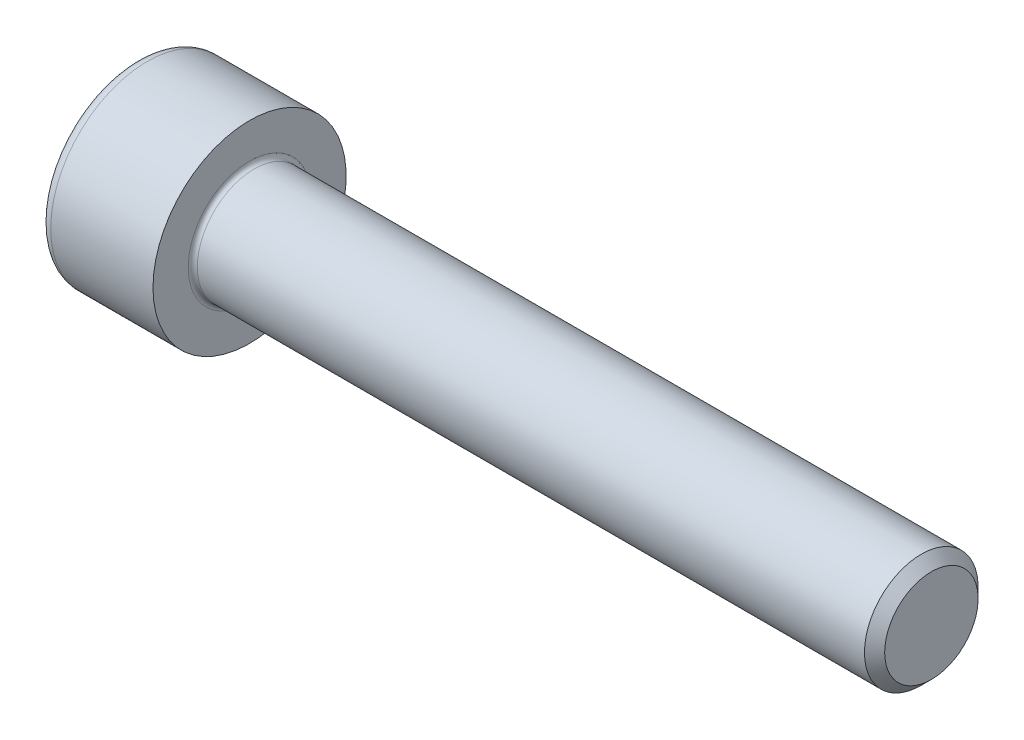
SolidWorks part; units mm, degrees
ref_plane "Plane1" through (0, 0, 0) normal (0, 0, 1) x (1, 0, 0)
ref_plane "Plane2" through (0, 0, 0) normal (0, 1, 0) x (1, 0, 0)
ref_plane "Plane3" through (0, 0, 0) normal (1, 0, 0) x (0, 0, -1)
sketch "BodySke" plane through (0, 0, 0) normal (0, 0, 1) x (1, 0, 0)
  line L0 (0, 0) -> (0, 4.25)
  line L1 (0, 4.25) -> (5, 4.25)
  line L2 (5, 4.25) -> (5, 2.5)
  line L3 (5, 2.5) -> (34.555, 2.5)
  line L4 (35, 2.055) -> (35, 0)
  line L5 (35, 0) -> (0, 0)
  line L6 (-31.75, 0) -> (127, 0) construction
  line L8 (35, 2.055) -> (34.555, 2.5)
  line L10 (35, -2.055) -> (34.555, -2.5) construction
  line L11 (5.8, 9.525) -> (5.8, 3.175) construction
  line L12 (5, 9.525) -> (5, 3.175) construction
  line L13 (-25, 9.525) -> (-25, 3.175) construction
  dimension "Diameter" = 5
  dimension "Head_ht" = 5
  dimension "Length" = 30
  dimension "Body_ch_ang" = 45
  dimension "Head_dia" = 8.5
  dimension "Minor_dia" = 4.11
  dimension "Advance" = 0.8
  dimension "Thread_nom" = 30
  dimension "Thread_length" = 60
revolve "Base-Revolve" add sketch "BodySke"
cosmetic thread "ThreadCosmetic"
fillet "Fillet1" radius 0.2 1 edges at (5, 0, 2.5)
fillet "Fillet2" radius 0.5 1 edges at (0, 0, 4.25)
sketch "Sketch2" plane through (0, 0, 0) normal (0, 0, 1) x (1, 0, 0)
  line L0 (0, 2.01) -> (2.5, 2.01)
  line L1 (2.5, 2.01) -> (3.6605, 0)
  line L2 (-31.75, 0) -> (127, 0) construction
  line L3 (3.6605, 0) -> (0, 0)
  line L4 (0, 0) -> (0, 2.01)
  line L6 (0, 0) -> (47.625, 0) construction
  dimension "D1" = 2.01
  dimension "D2" = 60
  dimension "Depth" = 2.5
revolve "Hex-PreBroach" cut sketch "Sketch2" angle 360 about L6
sketch "Sketch3" plane through (0, 0, 0) normal (-1, 0, 0) x (0, 0.5, 0.866)
  line L0 (1.1605, 2.01) -> (-1.1605, 2.01)
  line L1 (-1.1605, 2.01) -> (-2.3209, 0)
  line L2 (1.1605, 2.01) -> (2.3209, 0)
  line L3 (1.1605, -2.01) -> (2.3209, 0)
  line L4 (1.1605, -2.01) -> (-1.1605, -2.01)
  line L5 (-1.1605, -2.01) -> (-2.3209, 0)
  dimension "D1" = 2.01
  dimension "D2" = 2.01
  dimension "Hex_size" = 4.02
extrude "Hex" cut sketch "Sketch3" against normal blind 2.5
sketch "ThdSchSke" plane through (0, 0, 0) normal (0, 0, 1) x (1, 0, 0)
  line L0 (7.4, -2.055) -> (7.0884, -2.5)
  line L1 (7.4, -2.055) -> (7.7116, -2.5)
  line L2 (7.7116, -2.5) -> (7.7116, -3.125)
  line L3 (-3.175, 0) -> (5.1513, 0) construction
  line L4 (0, 3.75) -> (0, -3.75) construction
  line L5 (7.7116, -3.125) -> (7.0884, -3.125)
  line L6 (7.0884, -3.125) -> (7.0884, -2.5)
  dimension "Thread_minor" = 4.11
  dimension "Diameter" = 5
  dimension "Start" = 7.4
  dimension "SideAngle" = 55
  dimension "VeeAngle" = 70
  dimension "Overcut" = 6.25
revolve "ThreadSchematic" [suppressed] cut sketch "ThdSchSke" angle 360 about L3
pattern_linear "ThdSchPat" [suppressed]
equation "\"D2@Sketch3\" = \"Hex_size@Sketch3\" / 2"
equation "\"D1@Sketch3\" = \"Hex_size@Sketch3\" / 2"
equation "\"D1@Sketch2\" = \"Hex_size@Sketch3\" / 2"
equation "\"Thread_minor@ThreadCosmetic\"  =  \"Minor_dia@BodySke\""
equation "\"Depth@Sketch2\" =  \"Key_eng@Hex\""
equation "\"Thread_length@ThreadCosmetic\" = ((sgn( (\"Length@BodySke\" - \"Advance@BodySke\" * 3.0) - \"Thread_nom@BodySke\" )-1)*( (\"Length@BodySke\" - \"Advance@BodySke\" * 3.0) - \"Thread_nom@BodySke\" ))/-2+ \"Thread_nom@BodySke\""
equation "\"Thread_minor@ThdSchSke\" = \"Minor_dia@BodySke\""
equation "\"Diameter@ThdSchSke\" = \"Diameter@BodySke\""
equation "\"Overcut@ThdSchSke\" = \"Diameter@BodySke\" * 1.25"
equation "\"Start@ThdSchSke\" = \"Head_ht@BodySke\" + \"Length@BodySke\" - \"Thread_length@ThreadCosmetic\"  '---Non-countersunk---"
equation "\"Num_threads@ThdSchPat\" = int( \"Thread_length@ThreadCosmetic\" / \"Advance@BodySke\" + 0.999 )  + 1"
equation "\"Advance@ThdSchPat\" = \"Thread_length@ThreadCosmetic\" /  (\"Num_threads@ThdSchPat\" - 1) 'relax it"
equation "\"Num_threads@ThdSchPat\" = \"Num_threads@ThdSchPat\" - sgn( \"Num_threads@ThdSchPat\" - 1) '---chamfered tips only---"
